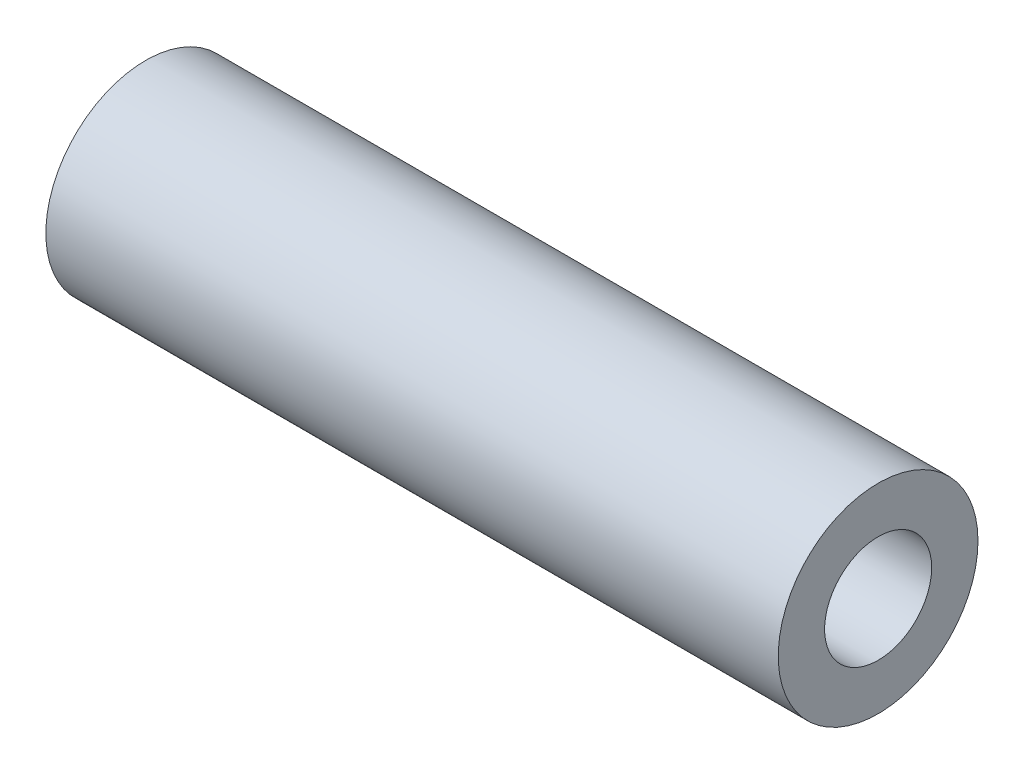
SolidWorks part; units mm, degrees
material "6061-T6 (SS)"
ref_plane "Front Plane" through (0, 0, 0) normal (0, 0, 1) x (1, 0, 0)
ref_plane "Top Plane" through (0, 0, 0) normal (0, 1, 0) x (1, 0, 0)
ref_plane "Right Plane" through (0, 0, 0) normal (1, 0, 0) x (0, 0, -1)
sketch "Sketch1" plane through (0, 0, 0) normal (1, 0, 0) x (0, 0, -1)
  circle A0 centre (0, 0) radius 2.5527
  circle A1 centre (0, 0) radius 4.7625
  dimension "D1" = 5.1054
  dimension "D2" = 9.525
extrude "Boss-Extrude1" add sketch "Sketch1" along normal blind 34.925
